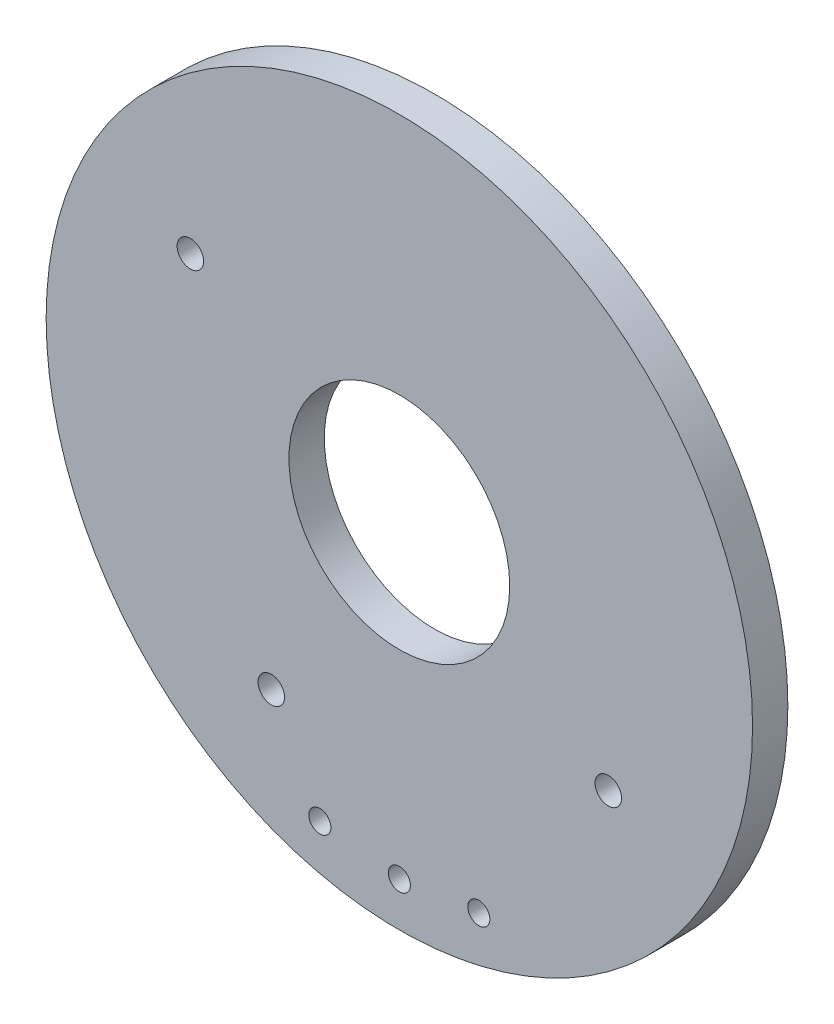
SolidWorks part; units mm, degrees
material "Fibra de vidrio-S"
ref_plane "Alzado" through (0, 0, 0) normal (0, 0, 1) x (1, 0, 0)
ref_plane "Planta" through (0, 0, 0) normal (0, 1, 0) x (1, 0, 0)
ref_plane "Vista lateral" through (0, 0, 0) normal (1, 0, 0) x (0, 0, -1)
sketch "Croquis1" plane through (0, 0, 0) normal (0, 0, 1) x (1, 0, 0)
  circle A0 centre (0, 0) radius 8
  circle A1 centre (0, 0) radius 2.5
  dimension "D1" = 5
  dimension "D2" = 16
extrude "Saliente-Extruir1" add sketch "Croquis1" along normal blind 0.8
sketch "Croquis2" plane through (0, 0, 0.8) normal (0, 0, 1) x (1, 0, 0)
  line L0 (0, -7) -> (0, 0) construction
  line L1 (0, 0) -> (-1.8, -6.7646) construction
  line L2 (-1.8, -6.7646) -> (0, -7) construction
  line L3 (0, 0) -> (1.8, -6.7646) construction
  line L4 (1.8, -6.7646) -> (0, -7) construction
  circle A0 centre (0, -7) radius 0.25
  circle A1 centre (-1.8, -6.7646) radius 0.25
  circle A2 centre (1.8, -6.7646) radius 0.25
  circle A3 centre (4.733, -2.9) radius 0.3
  circle A5 centre (-2.9, -4.733) radius 0.3
  circle A6 centre (-4.733, 2.9) radius 0.3
  circle A7 centre (2.9, 4.733) radius 0.3 [skipped]
  circle A9 centre (0, 0) radius 8 construction
  point P12 (-3.0399, -5.3496)
  point P13 (0, 0)
  point P21 (0, 0)
  dimension "D1" = 0.5
  dimension "D4" = 0.6
  dimension "D2" = 7
  dimension "D3" = 3.6
  dimension "D6" = 2.9
  dimension "D7" = 4.733
  dimension "D5" = 4
extrude "Cortar-Extruir1" cut sketch "Croquis2" against normal blind 1.6
